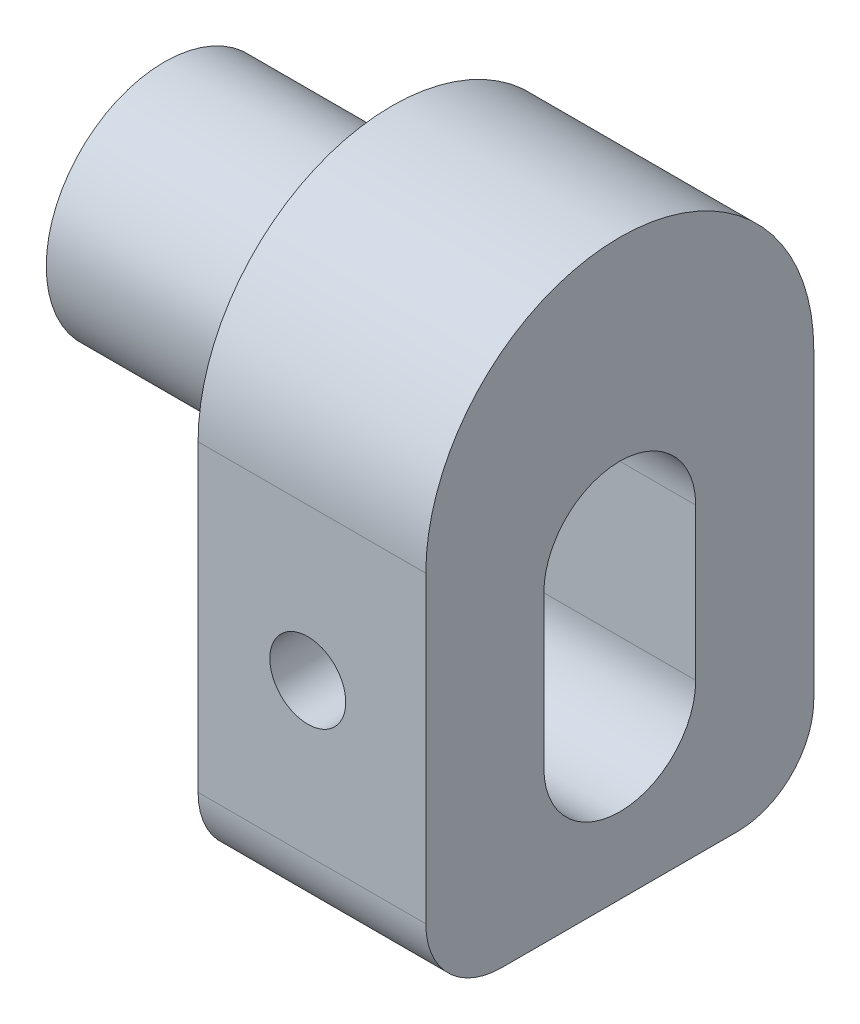
SolidWorks part; units mm, degrees
ref_plane "Front Plane" through (0, 0, 0) normal (0, 0, 1) x (1, 0, 0)
ref_plane "Top Plane" through (0, 0, 0) normal (0, 1, 0) x (1, 0, 0)
ref_plane "Right Plane" through (0, 0, 0) normal (1, 0, 0) x (0, 0, -1)
sketch "Sketch1" plane through (0, 0, 0) normal (1, 0, 0) x (0, 0, -1)
  circle A0 centre (0, 0) radius 3.95
  dimension "D1" = 7.9
extrude "Boss-Extrude1" add sketch "Sketch1" along normal blind 7.62
sketch "Sketch2" plane through (7.62, 0, 0) normal (1, 0, 0) x (0, 0, -1)
  line L2 (-3.95, 0) -> (-3.95, -10.16)
  line L3 (-3.95, -10.16) -> (3.95, -10.16)
  line L4 (3.95, 0) -> (3.95, -10.16)
  circle A0 centre (0, 0) radius 3.95 construction
  arc A1 (-3.95, 0) -> (3.95, 0) centre (0, 0) cw
  dimension "D1" = 10.16
extrude "Boss-Extrude2" add sketch "Sketch2" along normal blind 7.62
sketch "Sketch4" plane through (15.24, 0, 0) normal (1, 0, 0) x (0, 0, -1)
  line L16 (-6.49, 0) -> (-6.49, -12.7)
  line L17 (-6.49, -12.7) -> (6.49, -12.7)
  line L18 (6.49, -12.7) -> (6.49, 0)
  line L19 (-3.95, 0) -> (-3.95, -10.16)
  line L20 (-3.95, -10.16) -> (3.95, -10.16)
  line L21 (3.95, -10.16) -> (3.95, 0)
  line L22 (-3.95, 0) -> (-3.95, -10.16)
  line L23 (-3.95, -10.16) -> (3.95, -10.16)
  line L24 (3.95, -10.16) -> (3.95, 0)
  arc A0 (6.49, 0) -> (-6.49, 0) centre (0, 0) ccw
  arc A1 (3.95, 0) -> (-3.95, 0) centre (0, 0) ccw
  arc A2 (3.95, 0) -> (-3.95, 0) centre (0, 0) ccw
  point P0 (0, -6.5027)
  dimension "D3" = 0
  dimension "D4" = 2.54
extrude "Boss-Extrude3" add sketch "Sketch4" against normal up to surface (7.62 mm away) up to face at (7.62, -6.0675, 0)
sketch "Sketch5" plane through (15.24, 0, 0) normal (1, 0, 0) x (0, 0, -1)
  line L0 (-6.49, 0) -> (-6.49, -12.7) construction
  line L2 (-2.54, -2.54) -> (-2.54, -7.62)
  line L4 (2.54, -2.54) -> (2.54, -7.62)
  arc A0 (-2.54, -2.54) -> (2.54, -2.54) centre (0, -2.54) cw
  arc A1 (-2.54, -7.62) -> (2.54, -7.62) centre (0, -7.62) ccw
  dimension "D1" = 5.08
  dimension "D2" = 5.08
  dimension "D3" = 3.95
extrude "Cut-Extrude1" cut sketch "Sketch5" against normal blind 7.62
sketch "Sketch6" plane through (0, 0, 2.54) normal (0, 0, -1) x (-1, 0, 0)
  line L0 (-11.291, -2.54) -> (-11.291, -7.62) construction
  line L1 (-7.62, -2.54) -> (-15.24, -2.54) construction
  line L2 (-7.62, -7.62) -> (-15.24, -7.62) construction
  circle A0 centre (-11.291, -5.08) radius 1.27
  point P8 (-12.561, -5.08)
  dimension "D1" = 2.54
extrude "Cut-Extrude2" cut sketch "Sketch6" against normal through all
sketch "Sketch7" plane through (7.62, 0, 0) normal (-1, 0, 0) x (0, 0, 1)
  circle A0 centre (0, 0) radius 4.445
  dimension "D1" = 8.89
extrude "Boss-Extrude4" add sketch "Sketch7" along normal blind 1.27
fillet "Fillet1" radius 2.54 2 edges at (11.43, -12.7, -6.49) (11.43, -12.7, 6.49)
